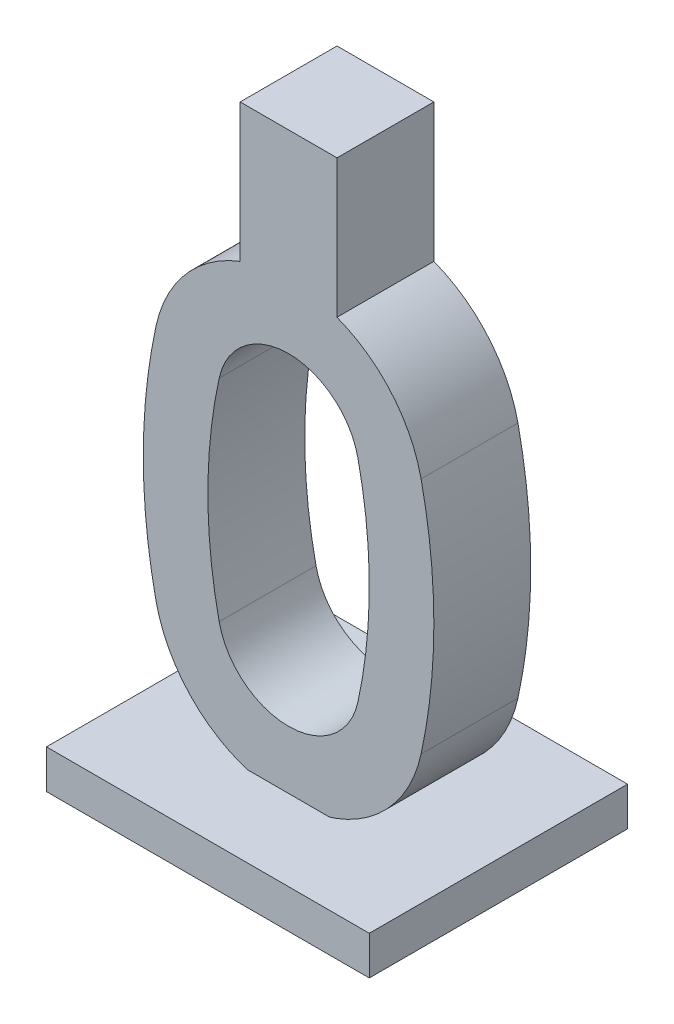
SolidWorks part; units mm, degrees
ref_plane "Vorne" through (0, 0, 0) normal (0, 0, 1) x (1, 0, 0)
ref_plane "Oben" through (0, 0, 0) normal (0, 1, 0) x (1, 0, 0)
ref_plane "Rechts" through (0, 0, 0) normal (1, 0, 0) x (0, 0, -1)
sketch "Skizze1" plane through (0, 0, 0) normal (0, 0, 1) x (1, 0, 0)
  line L0 (0, 64.0914) -> (0, -64.0914) construction
  line L1 (-65.0409, 0) -> (66.9399, 0) construction
  arc A3 (20.5233, 18.4489) -> (-20.5233, 18.4489) centre (0, 14) ccw
  arc A4 (-20.5233, 18.4489) -> (-20.5233, -18.4489) centre (64.5833, 0) ccw
  arc A5 (-20.5233, -18.4489) -> (20.5233, -18.4489) centre (0, -14) ccw
  arc A6 (20.5233, 18.4489) -> (20.5233, -18.4489) centre (-64.5833, 0) cw
  arc A7 (10.7503, 16.3304) -> (-10.7503, 16.3304) centre (0, 14) ccw
  arc A8 (-10.7503, 16.3304) -> (-10.7503, -16.3304) centre (64.5833, 0) ccw
  arc A9 (-10.7503, -16.3304) -> (0, -25) centre (0, -14) ccw
  arc A10 (10.7503, -16.3304) -> (0, -25) centre (0, -14) cw
  arc A11 (10.7503, 16.3304) -> (10.7503, -16.3304) centre (-64.5833, 0) cw
  point P14 (-22.5, 0)
  point P15 (22.5, 0)
  dimension "D1" = 45
  dimension "D2" = 70
  dimension "D3" = 50
  dimension "D4" = 14
extrude "Aufsatz-Linear austragen1" add sketch "Skizze1" along normal blind 15
ref_plane "Ebene1" through (0, -35, 0) normal (0, 1, 0) x (1, 0, 0)
sketch "Skizze2" plane through (0, -35, 0) normal (0, 1, 0) x (1, 0, 0)
  line L0 (0, -50.7189) -> (0, 37.3078) construction
  line L1 (-25, -27.5) -> (25, -27.5)
  line L2 (-25, -27.5) -> (-25, 12.5)
  line L3 (-25, 12.5) -> (25, 12.5)
  line L4 (25, -27.5) -> (25, 12.5)
  line L5 (-54.663, -7.5) -> (67.8434, -7.5) construction
  line L6 (20.5233, 0) -> (-20.5233, 0) construction
  line L7 (-20.5233, -15) -> (20.5233, -15) construction
  dimension "D1" = 40
  dimension "D2" = 50
extrude "Aufsatz-Linear austragen2" add sketch "Skizze2" against normal blind 5 and the other way blind 1 separate body
sketch "Skizze3" plane through (0, 0, 15) normal (0, 0, 1) x (1, 0, 0)
  line L0 (0, 51.0243) -> (0, -12.2475) construction
  line L1 (-7.5, 55) -> (7.5, 55)
  line L2 (-7.5, 55) -> (-7.5, 33.615)
  line L3 (-7.5, 33.615) -> (7.5, 33.615)
  line L4 (7.5, 55) -> (7.5, 33.615)
  arc A0 (20.5233, 18.4489) -> (-20.5233, 18.4489) centre (0, 14) ccw construction
  dimension "D1" = 20
  dimension "D2" = 15
extrude "Aufsatz-Linear austragen3" add sketch "Skizze3" against normal blind 15
